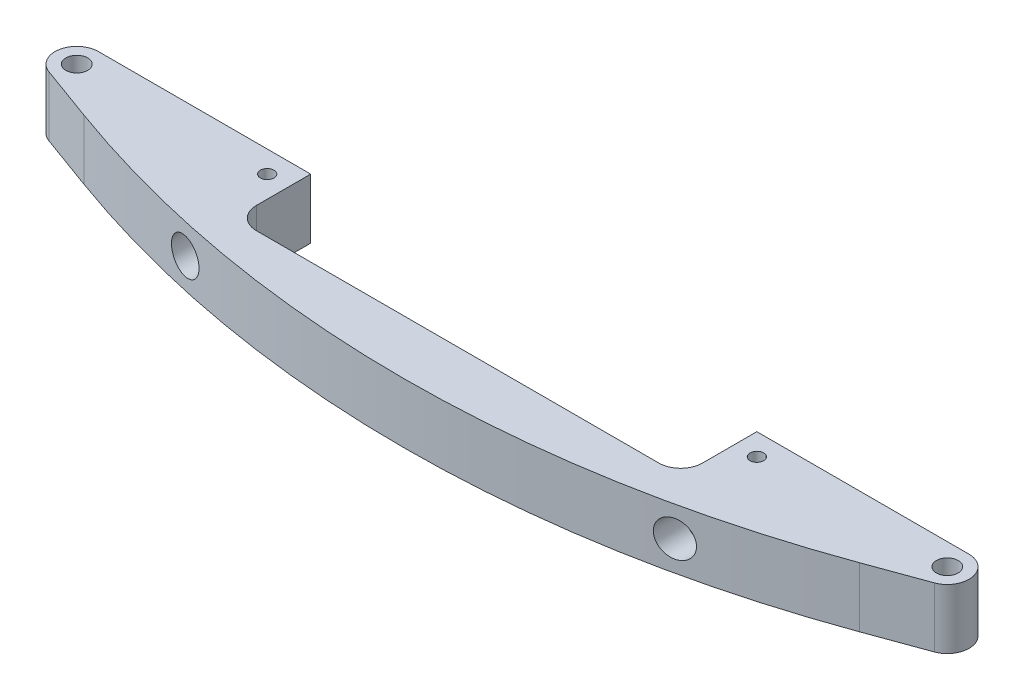
SolidWorks part; units mm, degrees
material "2014-T6"
ref_plane "Ebene vorne" through (0, 0, 0) normal (0, 0, 1) x (1, 0, 0)
ref_plane "Ebene oben" through (0, 0, 0) normal (0, 1, 0) x (1, 0, 0)
ref_plane "Ebene rechts" through (0, 0, 0) normal (1, 0, 0) x (0, 0, -1)
sketch "Skizze1" plane through (0, 0, 0) normal (0, 1, 0) x (1, 0, 0)
  line L0 (0, 87.9519) -> (0, -34.7709) construction
  line L1 (80, 0) -> (-80, 0) construction
  line L2 (-80, 4) -> (-45, 4)
  line L3 (-81.3681, -3.7588) -> (-71.2753, -7.4322)
  line L4 (0, -20) -> (0, -10)
  line L5 (-41, -10) -> (0, -10)
  line L6 (-41, 4) -> (-41, -10)
  line L8 (-45, 4) -> (-41, 4)
  arc A0 (-80, 4) -> (-81.3681, -3.7588) centre (-80, 0) ccw
  arc A1 (-71.2753, -7.4322) -> (0, -20) centre (0, 188.395) ccw
  circle A2 centre (-80, 0) radius 2
  dimension "D2" = 160
  dimension "D9" = 20
  dimension "D3" = 8
  dimension "D10" = 4
  dimension "D4" = 90
  dimension "D5" = 20
  dimension "D6" = 4
  dimension "D8" = 10
extrude "Aufsatz-Linear austragen1" add sketch "Skizze1" along normal mid plane 11
fillet "Verrundung1" radius 4 1 edges at (-41, 0, 10)
hole_wizard "M3 Gewindebohrung1" positions "Skizze6" profile "Skizze5" tap size "M3" standard "DIN" end condition through all
sketch "Skizze6" plane through (0, 5.5, 0) normal (0, 1, 0) x (1, 0, 0)
  line L0 (-45, 0) -> (-41, 0) construction
  line L1 (-41, 4) -> (-41, -6) construction
  line L3 (-45, 4) -> (-45, 0) construction
  line L4 (-80, 4) -> (-41, 4) construction
  point P0 (-45, 0)
  dimension "D1" = 4
cosmetic thread "Bohrungsgewinde1" parameters "D2"=3
sketch "Skizze5" plane through (-45, 5.5, 0) normal (1, 0, 0) x (0, 0, 1)
  line L0 (0, 0) -> (0, 11)
  line L1 (0, 11) -> (1.25, 11)
  line L2 (1.25, 11) -> (1.25, 0)
  line L5 (1.25, 0) -> (0, 0)
  line L11 (0, -6.35) -> (0, 107.95) construction
  dimension "Bohrerdurchmesser" = 2.5
  dimension "Bohrungstiefe" = 11
mirror "Spiegeln3" about plane through (0, 0, 0) normal (1, 0, 0) of bodies 109 101
ref_plane "Ebene1" through (0, 0, 20) normal (0, 0, 1) x (1, 0, 0)
hole_wizard "Stirnsenkung für  M3 Zylinderschraube mit Schlitz/Kreuzschlitz1" positions "Skizze4" profile "Skizze3" counterbore size "M3" standard "DIN" end condition through all
sketch "Skizze4" plane through (0, 0, 20) normal (0, 0, 1) x (1, 0, 0)
  line L0 (-45, 0) -> (45, 0) construction
  line L2 (-41, 5.5) -> (-41, -5.5) construction
  point P0 (-45, 0)
  point P2 (45, 0)
  dimension "D1" = 4
sketch "Skizze3" plane through (-45, 0, 20) normal (1, 0, 0) x (0, -1, 0)
  line L0 (0, 0) -> (0, 24)
  line L1 (0, 24) -> (1.6, 24)
  line L3 (1.6, 24) -> (1.6, 10)
  line L4 (1.6, 10) -> (3.25, 10)
  line L5 (3.25, 10) -> (3.25, 0)
  line L7 (3.25, 0) -> (0, 0)
  line L11 (0, -6.35) -> (0, 107.95) construction
  dimension "Bohrerdurchmesser" = 3.2
  dimension "Bohrungstiefe" = 24
  dimension "Senkdurchmesser2" = 6.5
  dimension "Senktiefe2" = 10
